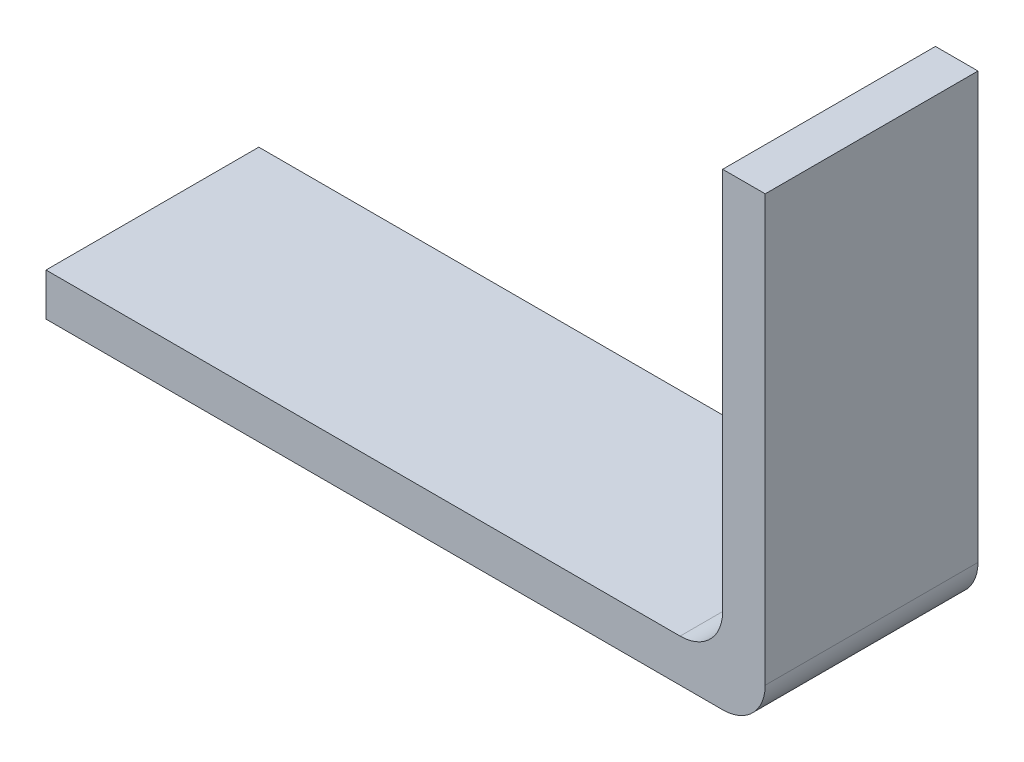
SolidWorks part; units mm, degrees
ref_plane "Front Plane" through (0, 0, 0) normal (0, 0, 1) x (1, 0, 0)
ref_plane "Top Plane" through (0, 0, 0) normal (0, 1, 0) x (1, 0, 0)
ref_plane "Right Plane" through (0, 0, 0) normal (1, 0, 0) x (0, 0, -1)
sketch "Sketch1" plane through (0, 0, 0) normal (0, 0, 1) x (1, 0, 0)
  line L0 (0, 0) -> (15.9, 0)
  line L1 (15.9, 0) -> (15.9, 10)
  dimension "D1" = 10
  dimension "D2" = 15.9
extrude "Extrude-Thin1" add sketch "Sketch1" along normal blind 5 thin
fillet "Fillet1" radius 1 2 edges at (15.9, 0, 2.5) (16.9, -1, 2.5)
